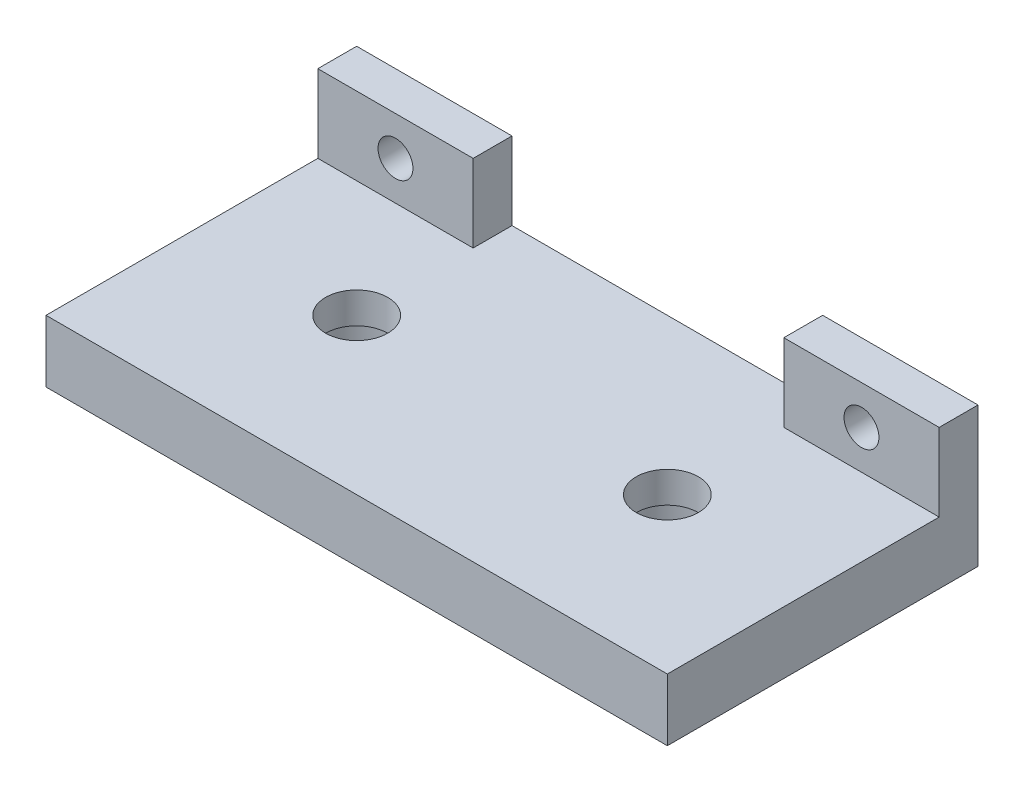
SolidWorks part; units mm, degrees
ref_plane "Front Plane" through (0, 0, 0) normal (0, 0, 1) x (1, 0, 0)
ref_plane "Top Plane" through (0, 0, 0) normal (0, 1, 0) x (1, 0, 0)
ref_plane "Right Plane" through (0, 0, 0) normal (1, 0, 0) x (0, 0, -1)
sketch "Sketch1" plane through (0, 0, 0) normal (0, 1, 0) x (1, 0, 0)
  line L1 (-40.2026, -33.3385) -> (39.7974, -33.3385)
  line L2 (-40.2026, -33.3385) -> (-40.2026, 6.6615)
  line L3 (-40.2026, 6.6615) -> (39.7974, 6.6615)
  line L4 (39.7974, -33.3385) -> (39.7974, 6.6615)
  dimension "D1" = 80
  dimension "D2" = 40
extrude "Boss-Extrude1" add sketch "Sketch1" along normal blind 8
sketch "Sketch2" plane through (0, 8, 0) normal (0, 1, 0) x (1, 0, 0)
  line L0 (-40.2026, -33.3385) -> (39.7974, -33.3385) construction
  line L1 (39.7974, -33.3385) -> (39.7974, 6.6615) construction
  line L2 (-40.2026, 6.6615) -> (-40.2026, -33.3385) construction
  circle A0 centre (19.7974, -13.3385) radius 4
  circle A1 centre (-20.2026, -13.3385) radius 4
  dimension "D1" = 20
  dimension "D2" = 20
  dimension "D3" = 20
  dimension "D4" = 20
extrude "Cut-Extrude1" cut sketch "Sketch2" against normal blind 4
sketch "Sketch3" plane through (0, 8, 0) normal (0, 1, 0) x (1, 0, 0)
  line L0 (39.7974, 6.6615) -> (-40.2026, 6.6615) construction
  line L1 (39.7974, 1.6615) -> (19.7974, 1.6615)
  line L2 (39.7974, 1.6615) -> (39.7974, 6.6615)
  line L3 (39.7974, 6.6615) -> (19.7974, 6.6615)
  line L4 (19.7974, 1.6615) -> (19.7974, 6.6615)
  line L5 (39.7974, -33.3385) -> (39.7974, 6.6615) construction
  line L6 (-20.2026, 1.6615) -> (-40.2026, 1.6615)
  line L7 (-20.2026, 1.6615) -> (-20.2026, 6.6615)
  line L8 (-20.2026, 6.6615) -> (-40.2026, 6.6615)
  line L9 (-40.2026, 1.6615) -> (-40.2026, 6.6615)
  line L10 (-40.2026, 6.6615) -> (-40.2026, -33.3385) construction
  point P10 (39.7974, 4.1615)
  dimension "D1" = 0
  dimension "D2" = 0
  dimension "D3" = 20
  dimension "D4" = 20
  dimension "D5" = 5
  dimension "D6" = 5
extrude "Boss-Extrude2" add sketch "Sketch3" along normal blind 10
sketch "Sketch5" plane through (0, 0, 0) normal (0, -1, 0) x (-1, 0, 0)
  line L0 (-39.7974, 6.6615) -> (40.2026, 6.6615) construction
  line L1 (40.2026, 6.6615) -> (40.2026, -33.3385) construction
  line L2 (-39.7974, -33.3385) -> (-39.7974, 6.6615) construction
  circle A0 centre (20.2026, -13.3385) radius 5.75
  circle A1 centre (-19.7974, -13.3385) radius 5.75
  dimension "D1" = 20
  dimension "D2" = 20
  dimension "D3" = 20
  dimension "D4" = 20
extrude "Cut-Extrude3" cut sketch "Sketch5" against normal blind 4
hole_wizard "#8 Clearance Hole1" positions "3DSketch1" profile "Sketch6" hole size "#8" standard "ANSI Inch"
sketch3d "3DSketch1"
  line L0 (39.7974, 18, -6.6615) -> (19.7974, 18, -6.6615) construction
  line L1 (39.7974, 18, -6.6615) -> (39.7974, 0, -6.6615) construction
  line L2 (-40.2026, 18, -6.6615) -> (-40.2026, 0, -6.6615) construction
  line L3 (-20.2026, 18, -6.6615) -> (-40.2026, 18, -6.6615) construction
  point P0 (29.7974, 13, -6.6615)
  point P2 (-30.2026, 13, -6.6615)
  dimension "D1" = 5
  dimension "D2" = 10
  dimension "D3" = 10
  dimension "D4" = 5
sketch "Sketch6" plane through (29.7974, 13, -6.6615) normal (1, 0, 0) x (0, 1, 0)
  line L0 (0, 0) -> (0, 6.3507)
  line L1 (0, 6.3507) -> (2.2479, 5)
  line L2 (2.2479, 5) -> (2.2479, 0)
  line L5 (2.2479, 0) -> (0, 0)
  line L10 (0, 6.3507) -> (-2.2479, 5) construction
  line L11 (0, -6.35) -> (0, 107.95) construction
  dimension "Hole Dia." = 4.4958
  dimension "Hole Depth" = 5
  dimension "Drill Angle" = 118
